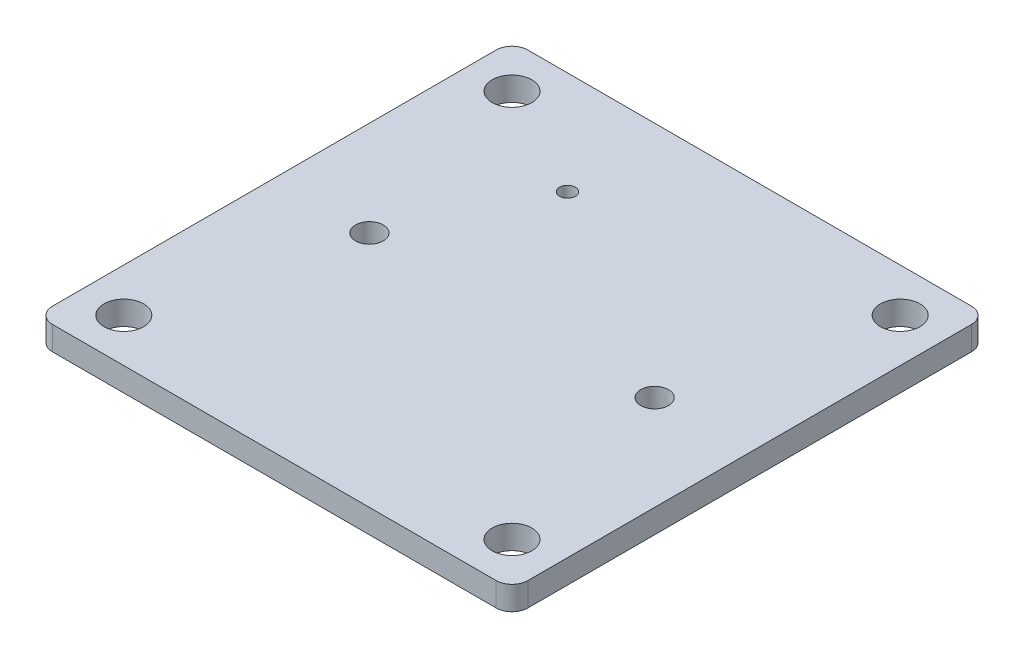
SolidWorks part; units mm, degrees
ref_plane "Front Plane" through (0, 0, 0) normal (0, 0, 1) x (1, 0, 0)
ref_plane "Top Plane" through (0, 0, 0) normal (0, 1, 0) x (1, 0, 0)
ref_plane "Right Plane" through (0, 0, 0) normal (1, 0, 0) x (0, 0, -1)
sketch "Sketch1" plane through (0, 0, 0) normal (0, 1, 0) x (1, 0, 0)
  line L0 (-15, 15) -> (15, -15) construction
  line L1 (-15, 15) -> (15, 15)
  line L2 (-15, 15) -> (-15, -15)
  line L3 (-15, -15) -> (15, -15)
  line L4 (15, 15) -> (15, -15)
  line L5 (15, 15) -> (-15, -15) construction
  line L7 (-12.25, 12.25) -> (12.25, 12.25) construction
  line L8 (-12.25, 12.25) -> (-12.25, -12.25) construction
  line L9 (-12.25, -12.25) -> (12.25, -12.25) construction
  line L10 (12.25, 12.25) -> (12.25, -12.25) construction
  circle A0 centre (-12.25, 12.25) radius 1.25
  circle A1 centre (12.25, 12.25) radius 1.25
  circle A2 centre (12.25, -12.25) radius 1.25
  circle A3 centre (-12.25, -12.25) radius 1.25
  dimension "D3" = 2.5
  dimension "D1" = 30
  dimension "D2" = 24.5
extrude "Boss-Extrude1" add sketch "Sketch1" along normal blind 1.5
fillet "Fillet1" radius 1 4 edges at (15, 0.75, 15) (15, 0.75, -15) (-15, 0.75, -15) (-15, 0.75, 15)
sketch "Sketch2" plane through (0, 1.5, 0) normal (0, 1, 0) x (1, 0, 0)
  line L0 (-15, 14) -> (-15, -14) construction
  line L1 (14, 15) -> (-14, 15) construction
  line L2 (-15, 0) -> (15, 0) construction
  line L3 (15, -14) -> (15, 14) construction
  line L4 (0, 15) -> (0, -15) construction
  line L5 (-14, -15) -> (14, -15) construction
  circle A0 centre (-5, 8.5) radius 0.5
  circle A1 centre (-9, 0) radius 0.875
  circle A2 centre (9, 0) radius 0.875
  dimension "D1" = 1
  dimension "D4" = 1.75
  dimension "D2" = 10
  dimension "D3" = 6.5
  dimension "D5" = 18
extrude "Cut-Extrude1" cut sketch "Sketch2" against normal through all
